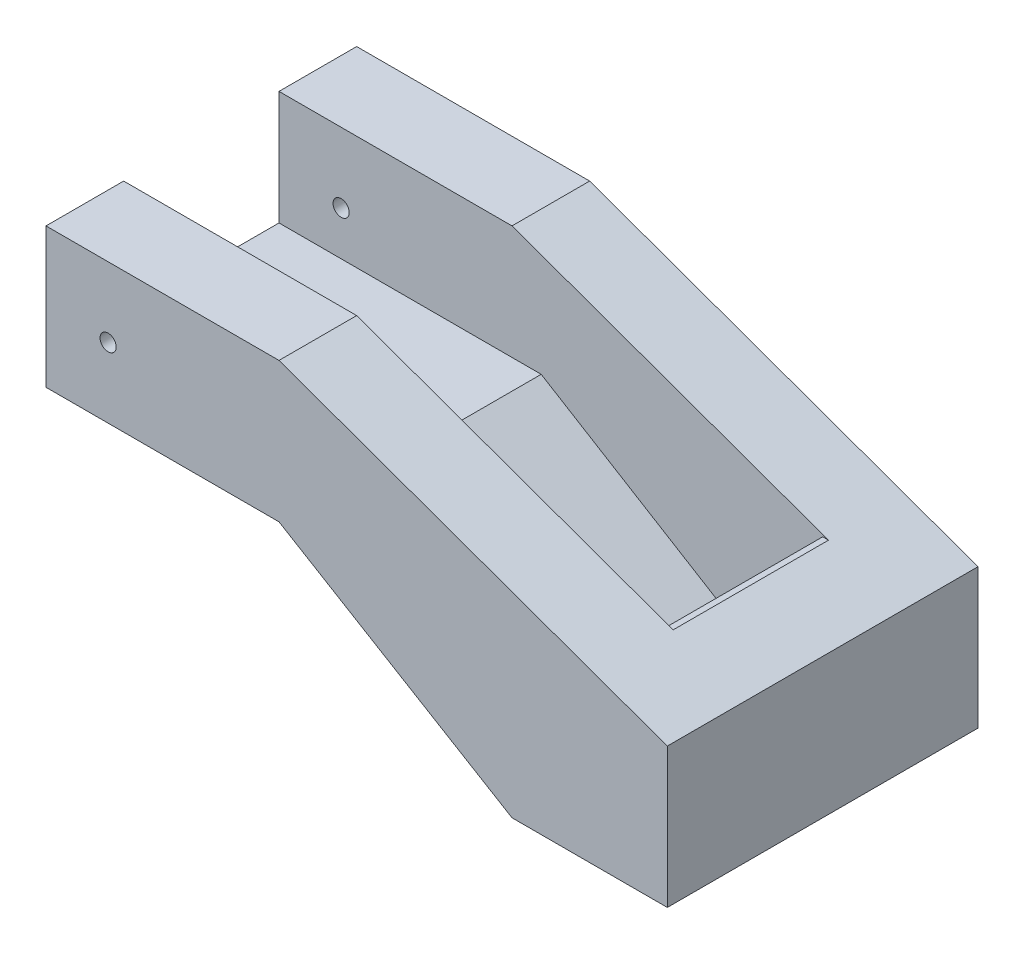
SolidWorks part; units mm, degrees
ref_plane "Front Plane" through (0, 0, 0) normal (0, 0, 1) x (1, 0, 0)
ref_plane "Top Plane" through (0, 0, 0) normal (0, 1, 0) x (1, 0, 0)
ref_plane "Right Plane" through (0, 0, 0) normal (1, 0, 0) x (0, 0, -1)
sketch "Sketch1" plane through (0, 0, 0) normal (0, 0, 1) x (1, 0, 0)
  line L1 (-254, 114.3) -> (254, 114.3)
  line L2 (-254, 114.3) -> (-254, -114.3)
  line L3 (-254, -114.3) -> (254, -114.3)
  line L4 (254, 114.3) -> (254, -114.3)
  line L5 (-254, 114.3) -> (254, -114.3) construction
  line L6 (-254, -114.3) -> (254, 114.3) construction
  point P0 (0, 0)
  dimension "D1" = 508
  dimension "D2" = 228.6
extrude "Boss-Extrude1" add sketch "Sketch1" along normal blind 254
sketch "Sketch2" plane through (-254, 0, 0) normal (-1, 0, 0) x (0, 0, 1)
  line L3 (254, 114.3) -> (0, 114.3) construction
  line L4 (63.5, 114.3) -> (63.5, 21.1457)
  line L6 (190.5, 114.3) -> (190.5, 21.1457)
  line L7 (63.5, 21.1457) -> (190.5, 21.1457)
  line L8 (63.5, 114.3) -> (190.5, 114.3)
extrude "Cut-Extrude1" cut sketch "Sketch2" against normal through all
sketch "Sketch5" plane through (0, 0, 254) normal (0, 0, 1) x (1, 0, 0)
  line L0 (-254, -114.3) -> (-254, 0)
  line L1 (-254, 114.3) -> (-63.5, 114.3)
  line L2 (254, 114.3) -> (-254, 114.3) construction
  line L3 (-254, 114.3) -> (-254, -114.3) construction
  line L5 (-254, 0) -> (254, 0)
  line L6 (254, -114.3) -> (254, 114.3) construction
  line L7 (-254, -114.3) -> (127, -114.3)
  line L8 (-254, -114.3) -> (254, -114.3) construction
  line L9 (254, -114.3) -> (127, -114.3)
  line L10 (127, -114.3) -> (-63.5, 0)
  line M7 (-254, 114.3) -> (-254, -114.3)
  line M8 (-254, -114.3) -> (254, -114.3)
extrude "Cut-Extrude2" cut sketch "Sketch5" against normal blind 254 contours L10 L5 M8 M7
sketch "Sketch7" plane through (254, 0, 0) normal (1, 0, 0) x (0, 0, -1)
  line L0 (-190.5, 21.1457) -> (-190.5, -80.4543)
  line L1 (-190.5, -80.4543) -> (-63.5, -80.4543)
  line L2 (-63.5, 21.1457) -> (-63.5, -80.4543)
  line L3 (-190.5, 21.1457) -> (-63.5, 21.1457)
extrude "Cut-Extrude3" cut sketch "Sketch7" against normal blind 127
sketch "Sketch15" plane through (127, 0, 0) normal (1, 0, 0) x (0, 0, -1)
  line L0 (-63.5, 21.1457) -> (-63.5, -80.4543)
  line L1 (-63.5, -80.4543) -> (-190.5, -80.4543)
  line L2 (-190.5, -80.4543) -> (-190.5, 21.1457)
  line L3 (-190.5, 21.1457) -> (-63.5, 21.1457)
sketch "Sketch16" plane through (0, 0, 254) normal (0, 0, 1) x (1, 0, 0)
  line L0 (127, -80.4543) -> (-39.7068, 21.1457)
  line L1 (127, -80.4543) -> (127, 21.1457) construction
  line L2 (-39.7068, 21.1457) -> (127, 21.1457)
  line L3 (127, 21.1457) -> (127, -80.4543)
  dimension "D1" = 166.7068
  dimension "D2" = 101.6
  dimension "D3" = 195.2273
sketch "Sketch18" plane through (0, 0, 254) normal (0, 0, 1) x (1, 0, 0)
  line L0 (127, 21.1457) -> (254, 21.1457)
  line L1 (254, -114.3) -> (254, 114.3) construction
sketch "Sketch19" plane through (254, 0, 0) normal (1, 0, 0) x (0, 0, -1)
  line L0 (-254, 21.1457) -> (-190.5, 21.1457)
  line L1 (-190.5, -80.4543) -> (-190.5, 114.3) construction
sketch "Sketch20" plane through (0, 0, 190.5) normal (0, 0, -1) x (-1, 0, 0)
  line L0 (-254, 21.1457) -> (-127, 21.1457)
  line L1 (-127, 21.1457) -> (39.624, 21.1457)
  line L2 (-127, 21.1457) -> (254, 21.1457) construction
  line L3 (39.624, 21.1457) -> (-127, -80.4543)
  line L4 (-127, 21.1457) -> (-127, -80.4543)
extrude "Cut-Extrude5" cut sketch "Sketch20" against normal blind 0.254 and the other way blind 127 contours L1 L3 L4
sketch "Sketch21" plane through (0, 0, 190.5) normal (0, 0, -1) x (-1, 0, 0)
  line L0 (-127, 21.1457) -> (-190.5, 21.1457)
  line L1 (-190.5, 21.1457) -> (-190.5, -80.4543)
  line L2 (-127, -80.4543) -> (-254, -80.4543) construction
sketch "Sketch22" plane through (0, -80.4543, 0) normal (0, 1, 0) x (1, 0, 0)
  line L0 (190.5, -190.5) -> (190.5, -63.5)
  line L1 (127, -63.5) -> (254, -63.5) construction
sketch "Sketch23" plane through (0, 0, 63.5) normal (0, 0, 1) x (1, 0, 0)
  line L0 (190.5, -80.4543) -> (190.5, 21.1457)
  line L1 (127, 21.1457) -> (190.5, 21.1457)
sketch "Sketch24" plane through (254, 0, 0) normal (1, 0, 0) x (0, 0, -1)
  line L0 (-190.5, 21.1457) -> (-63.5, 21.1457)
  line L1 (-63.5, 114.3) -> (-63.5, -80.4543) construction
  line L2 (-190.5, 21.1457) -> (-190.5, -80.4543)
  line L3 (-190.5, -80.4543) -> (-63.5, -80.4543)
  line L4 (-63.5, -80.4543) -> (-63.5, 21.1457)
extrude "Boss-Extrude3" add sketch "Sketch24" against normal blind 63.5
sketch "Sketch26" plane through (0, 0, 254) normal (0, 0, 1) x (1, 0, 0)
  line L0 (-63.5, 0) -> (-63.5, 114.3)
  line L1 (254, 114.3) -> (-254, 114.3) construction
  line L5 (-63.5, 114.3) -> (254, 0)
  line L6 (254, -114.3) -> (254, 114.3) construction
  line L7 (254, 0) -> (254, 114.3)
  line L8 (254, 114.3) -> (-63.5, 114.3)
  line L9 (-63.5, 114.3) -> (254, 114.3)
  line L10 (254, 0) -> (-63.5, 114.3)
  line M5 (254, -114.3) -> (254, 114.3)
  line M6 (254, 114.3) -> (-254, 114.3)
extrude "Cut-Extrude7" cut sketch "Sketch26" against normal blind 315.976 contours L5 M6 M5
sketch "Sketch27" plane through (0, 0, 254) normal (0, 0, 1) x (1, 0, 0)
  line L0 (-254, 0) -> (-203.2, 0)
  line L1 (-254, 0) -> (-63.5, 0) construction
  line L2 (-203.2, 0) -> (-203.2, 57.15)
  circle A0 centre (-203.2, 57.15) radius 6.604
  dimension "D1" = 13.208
extrude "Cut-Extrude8" cut sketch "Sketch27" against normal blind 315.976 contours A0
